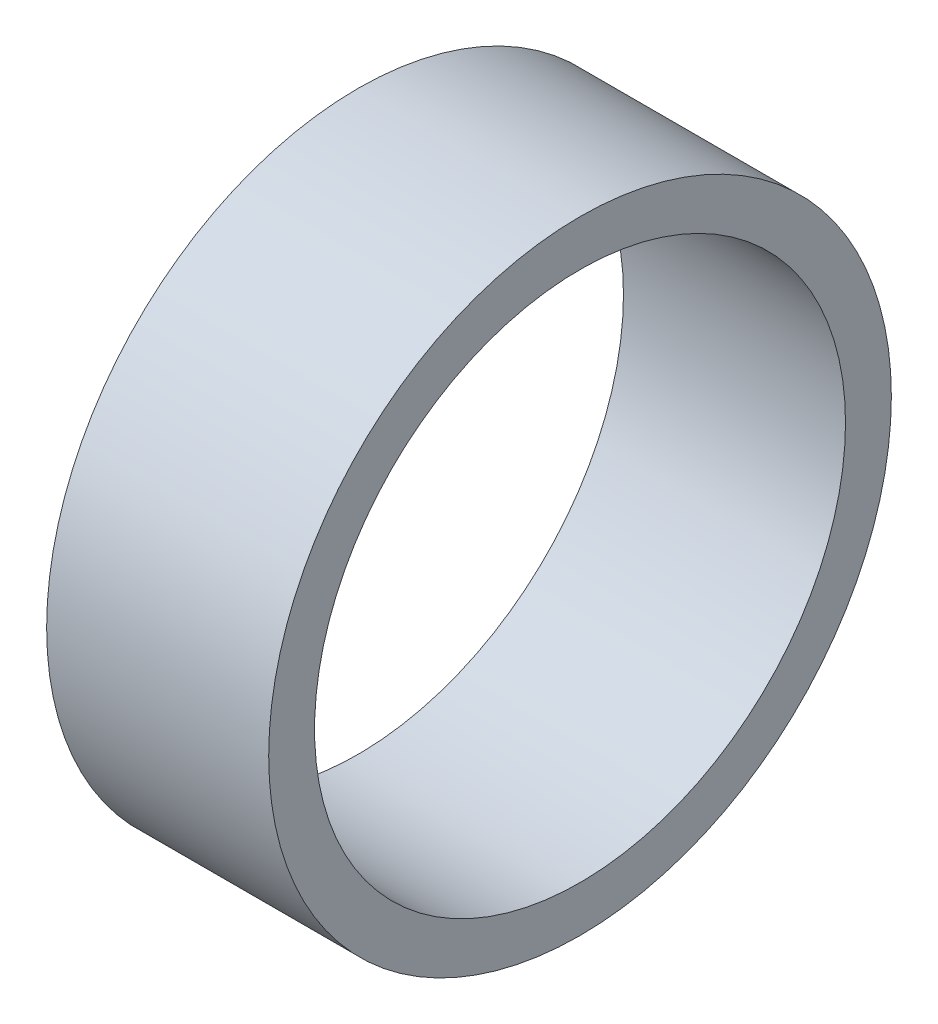
SolidWorks part; units mm, degrees
ref_plane "Front Plane" through (0, 0, 0) normal (0, 0, 1) x (1, 0, 0)
ref_plane "Top Plane" through (0, 0, 0) normal (0, 1, 0) x (1, 0, 0)
ref_plane "Right Plane" through (0, 0, 0) normal (1, 0, 0) x (0, 0, -1)
sketch "Sketch1" plane through (0, 0, 0) normal (1, 0, 0) x (0, 0, -1)
  circle A0 centre (0, 0) radius 32.25
  circle A1 centre (0, 0) radius 27.5
  dimension "D1" = 64.5
  dimension "D2" = 55
extrude "Boss-Extrude1" add sketch "Sketch1" along normal blind 23 contours A1 | A0
